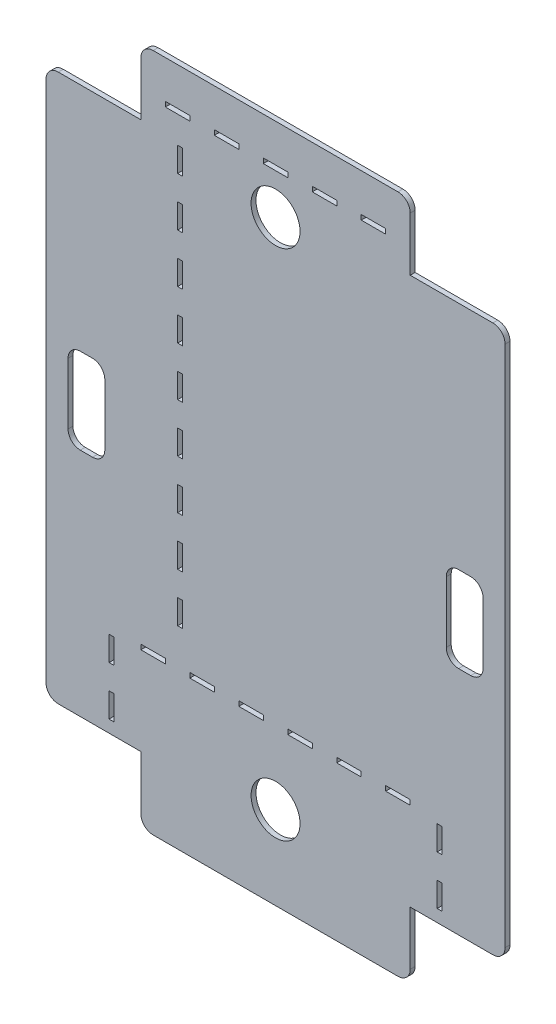
SolidWorks part; units mm, degrees
material "Verre"
ref_plane "Plan de face" through (0, 0, 0) normal (0, 0, 1) x (1, 0, 0)
ref_plane "Plan de dessus" through (0, 0, 0) normal (0, 1, 0) x (1, 0, 0)
ref_plane "Plan de droite" through (0, 0, 0) normal (1, 0, 0) x (0, 0, -1)
sketch "Esquisse1" plane through (0, 0, 0) normal (0, 0, 1) x (1, 0, 0)
  line L0 (-99.7487, 120) -> (-75, 144.7487)
  line L1 (-75, 144.7487) -> (75, 144.7487)
  line L2 (-99.7487, 120) -> (-99.7487, -120)
  line L3 (-75, -144.7487) -> (75, -144.7487)
  line L4 (99.7487, 120) -> (99.7487, -120)
  line L5 (75, 144.7487) -> (99.7487, 120)
  line L6 (99.7487, -120) -> (75, -144.7487)
  line L7 (-87.3744, 132.3744) -> (87.3744, -132.3744) construction
  line L8 (-99.7487, -120) -> (-75, -144.7487)
  line L9 (-87.3744, -132.3744) -> (87.3744, 132.3744) construction
  point P0 (0, 0)
  point P14 (0, 0)
  dimension "D1" = 240
  dimension "D2" = 150
  dimension "D3" = 35
  dimension "D4" = 135
  dimension "D5" = 135
extrude "Base" add sketch "Esquisse1" along normal blind 2
sketch "Esquisse2" plane through (0, 0, 2) normal (0, 0, 1) x (1, 0, 0)
  line L0 (-99.7487, 0) -> (99.7487, 0) construction
  line L1 (-99.7487, 120) -> (-99.7487, -120) construction
  line L2 (99.7487, -120) -> (99.7487, 120) construction
  line L3 (0, 144.7487) -> (0, -144.7487) construction
  line L4 (75, 144.7487) -> (-75, 144.7487) construction
  line L5 (-75, -144.7487) -> (75, -144.7487) construction
  line L6 (55, 131.7487) -> (55, 111.7487)
  line L7 (-75, 131.7487) -> (-55, 131.7487)
  line L8 (-75, 131.7487) -> (-75, 111.7487)
  line L9 (-75, 111.7487) -> (-55, 111.7487)
  line L10 (-55, 131.7487) -> (-55, 111.7487)
  line L11 (-75, 131.7487) -> (-55, 111.7487) construction
  line L12 (-75, 111.7487) -> (-55, 131.7487) construction
  line L13 (75, 111.7487) -> (55, 111.7487)
  line L14 (75, 131.7487) -> (75, 111.7487)
  line L15 (75, 131.7487) -> (55, 131.7487)
  line L16 (75, -111.7487) -> (55, -111.7487)
  line L17 (75, -131.7487) -> (75, -111.7487)
  line L18 (75, -131.7487) -> (55, -131.7487)
  line L19 (55, -131.7487) -> (55, -111.7487)
  line L20 (-55, -131.7487) -> (-55, -111.7487)
  line L21 (-75, -111.7487) -> (-55, -111.7487)
  line L22 (-75, -131.7487) -> (-75, -111.7487)
  line L23 (-75, -131.7487) -> (-55, -131.7487)
  point P12 (-65, 121.7487)
  dimension "D1" = 20
  dimension "D2" = 20
  dimension "D3" = 23
  dimension "D4" = 65
extrude "Perçage profilé" cut sketch "Esquisse2" against normal blind 5
sketch "Esquisse3" plane through (0, 0, 2) normal (0, 0, 1) x (1, 0, 0)
  line L0 (0, 144.7487) -> (0, -144.7487) construction
  line L1 (75, 144.7487) -> (-75, 144.7487) construction
  line L2 (-75, -144.7487) -> (75, -144.7487) construction
  line L3 (-99.7487, 0) -> (99.7487, 0) construction
  line L4 (-99.7487, 120) -> (-99.7487, -120) construction
  line L5 (99.7487, -120) -> (99.7487, 120) construction
  line L6 (79.7487, -17.5) -> (74.7487, -17.5)
  line L11 (-79.7487, 17.5) -> (-74.7487, 17.5)
  line L12 (-84.7487, 12.5) -> (-84.7487, -12.5)
  line L13 (-79.7487, -17.5) -> (-74.7487, -17.5)
  line L14 (-69.7487, 12.5) -> (-69.7487, -12.5)
  line L15 (-84.7487, 17.5) -> (-69.7487, -17.5) construction
  line L16 (-84.7487, -17.5) -> (-69.7487, 17.5) construction
  line L17 (84.7487, 12.5) -> (84.7487, -12.5)
  line L18 (79.7487, 17.5) -> (74.7487, 17.5)
  line L19 (69.7487, 12.5) -> (69.7487, -12.5)
  circle A0 centre (0, -104.7487) radius 10
  circle A1 centre (0, 104.7487) radius 10
  arc A2 (74.7487, -17.5) -> (69.7487, -12.5) centre (74.7487, -12.5) cw
  arc A3 (79.7487, -17.5) -> (84.7487, -12.5) centre (79.7487, -12.5) ccw
  arc A4 (84.7487, 12.5) -> (79.7487, 17.5) centre (79.7487, 12.5) ccw
  arc A5 (74.7487, 17.5) -> (69.7487, 12.5) centre (74.7487, 12.5) ccw
  arc A6 (-84.7487, -12.5) -> (-79.7487, -17.5) centre (-79.7487, -12.5) ccw
  arc A7 (-74.7487, -17.5) -> (-69.7487, -12.5) centre (-74.7487, -12.5) ccw
  arc A8 (-74.7487, 17.5) -> (-69.7487, 12.5) centre (-74.7487, 12.5) cw
  arc A9 (-79.7487, 17.5) -> (-84.7487, 12.5) centre (-79.7487, 12.5) ccw
  point P16 (-77.2487, 0)
  point P27 (69.7487, -17.5)
  point P30 (84.7487, -17.5)
  point P33 (84.7487, 17.5)
  point P36 (69.7487, 17.5)
  dimension "D1" = 20
  dimension "D6" = 5
  dimension "D2" = 15
  dimension "D3" = 35
  dimension "D4" = 40
  dimension "D5" = 15
extrude "Trous câble breadboard" cut sketch "Esquisse3" against normal blind 5
sketch "Sketch2" plane through (0, 0, 2) normal (0, 0, 1) x (1, 0, 0)
  line L0 (-55, 111.7487) -> (-55, 131.7487) construction
  line L1 (-45, 123.2487) -> (-35, 123.2487)
  line L2 (-45, 123.2487) -> (-45, 120.2487)
  line L3 (-45, 120.2487) -> (-35, 120.2487)
  line L4 (-35, 123.2487) -> (-35, 120.2487)
  line L5 (-75, 121.7487) -> (-55, 121.7487) construction
  line L6 (-75, 131.7487) -> (-75, 111.7487) construction
  line L7 (-45, 121.7487) -> (-35, 121.7487) construction
  line L8 (-25, 123.2487) -> (-25, 120.2487)
  line L9 (-25, 123.2487) -> (-15, 123.2487)
  line L10 (-15, 123.2487) -> (-15, 120.2487)
  line L11 (-25, 120.2487) -> (-15, 120.2487)
  line L12 (-5, 123.2487) -> (-5, 120.2487)
  line L13 (-5, 123.2487) -> (5, 123.2487)
  line L14 (5, 123.2487) -> (5, 120.2487)
  line L15 (-5, 120.2487) -> (5, 120.2487)
  line L16 (15, 123.2487) -> (15, 120.2487)
  line L17 (15, 123.2487) -> (25, 123.2487)
  line L18 (25, 123.2487) -> (25, 120.2487)
  line L19 (15, 120.2487) -> (25, 120.2487)
  line L20 (35, 123.2487) -> (35, 120.2487)
  line L21 (35, 123.2487) -> (45, 123.2487)
  line L22 (45, 123.2487) -> (45, 120.2487)
  line L23 (35, 120.2487) -> (45, 120.2487)
  line L24 (0, 0) -> (0, -37.251) construction
  line L25 (-68, -106.7487) -> (-65, -106.7487)
  line L26 (-68, -106.7487) -> (-68, -96.7487)
  line L27 (-68, -96.7487) -> (-65, -96.7487)
  line L28 (-65, -106.7487) -> (-65, -96.7487)
  line L29 (-55, -111.7487) -> (-75, -111.7487) construction
  line L30 (-66.5, -106.7487) -> (-66.5, -96.7487) construction
  line L31 (-40, 90.2487) -> (-40, 80.2487)
  line L32 (-40, 110.2487) -> (-37, 110.2487)
  line L33 (-68, -86.7487) -> (-68, -76.7487)
  line L34 (-68, -86.7487) -> (-65, -86.7487)
  line L35 (-65, -86.7487) -> (-65, -76.7487)
  line L36 (-68, -76.7487) -> (-65, -76.7487)
  line L37 (68, -86.7487) -> (65, -86.7487)
  line L38 (65, -86.7487) -> (65, -76.7487)
  line L39 (68, -76.7487) -> (65, -76.7487)
  line L40 (68, -86.7487) -> (68, -76.7487)
  line L41 (68, -96.7487) -> (65, -96.7487)
  line L42 (65, -106.7487) -> (65, -96.7487)
  line L43 (68, -106.7487) -> (65, -106.7487)
  line L44 (68, -106.7487) -> (68, -96.7487)
  line L45 (-35, -76.7487) -> (-35, -73.7487)
  line L46 (-55, -76.7487) -> (-45, -76.7487)
  line L47 (-55, -76.7487) -> (-55, -73.7487)
  line L48 (-55, -73.7487) -> (-45, -73.7487)
  line L49 (-45, -76.7487) -> (-45, -73.7487)
  line L50 (-35, -76.7487) -> (-25, -76.7487)
  line L51 (-25, -76.7487) -> (-25, -73.7487)
  line L52 (-35, -73.7487) -> (-25, -73.7487)
  line L53 (-15, -76.7487) -> (-15, -73.7487)
  line L54 (-15, -76.7487) -> (-5, -76.7487)
  line L55 (-5, -76.7487) -> (-5, -73.7487)
  line L56 (-15, -73.7487) -> (-5, -73.7487)
  line L57 (5, -76.7487) -> (5, -73.7487)
  line L58 (5, -76.7487) -> (15, -76.7487)
  line L59 (15, -76.7487) -> (15, -73.7487)
  line L60 (5, -73.7487) -> (15, -73.7487)
  line L61 (25, -76.7487) -> (25, -73.7487)
  line L62 (25, -76.7487) -> (35, -76.7487)
  line L63 (35, -76.7487) -> (35, -73.7487)
  line L64 (25, -73.7487) -> (35, -73.7487)
  line L65 (45, -76.7487) -> (45, -73.7487)
  line L66 (45, -76.7487) -> (55, -76.7487)
  line L67 (55, -76.7487) -> (55, -73.7487)
  line L68 (45, -73.7487) -> (55, -73.7487)
  line L69 (-40, 110.2487) -> (-40, 100.2487)
  line L70 (-40, 100.2487) -> (-37, 100.2487)
  line L71 (-37, 110.2487) -> (-37, 100.2487)
  line L72 (-40, 90.2487) -> (-37, 90.2487)
  line L73 (-37, 90.2487) -> (-37, 80.2487)
  line L74 (-40, 80.2487) -> (-37, 80.2487)
  line L75 (-40, 70.2487) -> (-40, 60.2487)
  line L76 (-40, 70.2487) -> (-37, 70.2487)
  line L77 (-37, 70.2487) -> (-37, 60.2487)
  line L78 (-40, 60.2487) -> (-37, 60.2487)
  line L79 (-40, 50.2487) -> (-40, 40.2487)
  line L80 (-40, 50.2487) -> (-37, 50.2487)
  line L81 (-37, 50.2487) -> (-37, 40.2487)
  line L82 (-40, 40.2487) -> (-37, 40.2487)
  line L83 (-40, 30.2487) -> (-40, 20.2487)
  line L84 (-40, 30.2487) -> (-37, 30.2487)
  line L85 (-37, 30.2487) -> (-37, 20.2487)
  line L86 (-40, 20.2487) -> (-37, 20.2487)
  line L87 (-40, 10.2487) -> (-40, 0.2487)
  line L88 (-40, 10.2487) -> (-37, 10.2487)
  line L89 (-37, 10.2487) -> (-37, 0.2487)
  line L90 (-40, 0.2487) -> (-37, 0.2487)
  line L91 (-40, -9.7513) -> (-40, -19.7513)
  line L92 (-40, -9.7513) -> (-37, -9.7513)
  line L93 (-37, -9.7513) -> (-37, -19.7513)
  line L94 (-40, -19.7513) -> (-37, -19.7513)
  line L95 (-40, -29.7513) -> (-40, -39.7513)
  line L96 (-40, -29.7513) -> (-37, -29.7513)
  line L97 (-37, -29.7513) -> (-37, -39.7513)
  line L98 (-40, -39.7513) -> (-37, -39.7513)
  line L99 (-40, -49.7513) -> (-40, -59.7513)
  line L100 (-40, -49.7513) -> (-37, -49.7513)
  line L101 (-37, -49.7513) -> (-37, -59.7513)
  line L102 (-40, -59.7513) -> (-37, -59.7513)
  dimension "D1" = 10
  dimension "D2" = 3
  dimension "D3" = 10
  dimension "D4" = 10
  dimension "D5" = 3
  dimension "D6" = 5
  dimension "D8" = 10
  dimension "D9" = 3
  dimension "D10" = 10
  dimension "D11" = 65
  dimension "D12" = 10
  dimension "D13" = 5
  dimension "D14" = 10
  dimension "D15" = 3
  dimension "D16" = 15
  dimension "D7" = 2
  dimension "D17" = 9
extrude "Cut-Extrude1" cut sketch "Sketch2" against normal through all
sketch "Esquisse5" plane through (0, 0, 2) normal (0, 0, 1) x (1, 0, 0)
  line L0 (-72.5147, 138.7487) -> (72.5147, 138.7487)
  line L1 (72.5147, 138.7487) -> (93.7487, 117.5147)
  line L2 (93.7487, 117.5147) -> (93.7487, -117.5147)
  line L3 (93.7487, -117.5147) -> (72.5147, -138.7487)
  line L4 (72.5147, -138.7487) -> (-72.5147, -138.7487)
  line L5 (-72.5147, -138.7487) -> (-93.7487, -117.5147)
  line L6 (-93.7487, -117.5147) -> (-93.7487, 117.5147)
  line L7 (-93.7487, 117.5147) -> (-72.5147, 138.7487)
  line L8 (75, 144.7487) -> (-75, 144.7487) construction
  line L9 (99.7487, 120) -> (75, 144.7487) construction
  line L10 (99.7487, -120) -> (99.7487, 120) construction
  line L11 (75, -144.7487) -> (99.7487, -120) construction
  line L12 (-75, -144.7487) -> (75, -144.7487) construction
  line L13 (-99.7487, -120) -> (-75, -144.7487) construction
  line L14 (-99.7487, 120) -> (-99.7487, -120) construction
  line L15 (-75, 144.7487) -> (-99.7487, 120) construction
  line L16 (-16.6743, 205.0451) -> (192.8195, 199.3251)
  line L17 (192.8195, 199.3251) -> (168.5096, -212.5125)
  line L18 (168.5096, -212.5125) -> (-168.9684, -176.7627)
  line L19 (-168.9684, -176.7627) -> (-185.4133, 175.0153)
  line L20 (-185.4133, 175.0153) -> (-16.6743, 205.0451)
  point P25 (-87.3744, 132.3744)
  dimension "D1" = 6
  dimension "D2" = 6
  dimension "D3" = 6
  dimension "D4" = 6
  dimension "D5" = 6
  dimension "D6" = 6
  dimension "D7" = 6
  dimension "D8" = 6
extrude "Enlèv. mat.-Extru.1" cut sketch "Esquisse5" against normal through all
sketch "Esquisse6" plane through (0, 0, 2) normal (0, 0, 1) x (1, 0, 0)
  line L0 (-55, 111.7487) -> (-55, 131.7487) construction
  line L1 (-55, 152.8346) -> (-122.6187, 152.8346)
  line L2 (-55, 152.8346) -> (-55, 111.7487)
  line L3 (-55, 111.7487) -> (-122.6187, 111.7487)
  line L4 (-122.6187, 152.8346) -> (-122.6187, 111.7487)
  line L6 (55, 131.7487) -> (55, 111.7487) construction
  line L7 (55, 111.7487) -> (108.2306, 111.7487)
  line L8 (55, 111.7487) -> (55, 146.7402)
  line L9 (55, 146.7402) -> (108.2306, 146.7402)
  line L10 (108.2306, 111.7487) -> (108.2306, 146.7402)
  line L13 (128.1315, -111.7487) -> (55, -111.7487)
  line L14 (128.1315, -111.7487) -> (128.1315, -148.2847)
  line L15 (128.1315, -148.2847) -> (55, -148.2847)
  line L16 (55, -111.7487) -> (55, -148.2847)
  line L17 (55, -111.7487) -> (55, -131.7487) construction
  line L19 (-104.2886, -111.7487) -> (-55, -111.7487)
  line L20 (-104.2886, -111.7487) -> (-104.2886, -146.9826)
  line L21 (-104.2886, -146.9826) -> (-55, -146.9826)
  line L22 (-55, -111.7487) -> (-55, -146.9826)
  line L23 (-55, -131.7487) -> (-55, -111.7487) construction
  line L24 (-55, -111.7487) -> (-75, -111.7487) construction
  line L25 (-75, 111.7487) -> (-55, 111.7487) construction
  line L26 (55, 111.7487) -> (75, 111.7487) construction
  line L27 (75, -111.7487) -> (55, -111.7487) construction
extrude "Enlèv. mat.-Extru.2" cut sketch "Esquisse6" against normal through all
fillet "Congé2" radius 5 4 edges at (55, -138.7487, 1) (-55, -138.7487, 1) (-55, 138.7487, 1) (55, 138.7487, 1)
sketch "Esquisse4" plane through (0, 0, 2) normal (0, 0, 1) x (1, 0, 0)
  line L1 (99.7487, 62.0019) -> (62.7487, 62.0019)
  line L2 (99.7487, 62.0019) -> (99.7487, -32.9981)
  line L3 (99.7487, -32.9981) -> (62.7487, -32.9981)
  line L4 (62.7487, 62.0019) -> (62.7487, -32.9981)
  line L5 (41.9383, 53.5019) -> (39.3294, 53.5019) construction
  line L6 (38.7442, 53.5019) -> (38.7442, 62.0019) construction
  line L7 (84.0538, -24.4981) -> (84.0538, -32.9981) construction
  line L8 (49.6874, -24.4981) -> (43.4757, -24.4981) construction
  line L10 (62.7487, 62.0019) -> (29.7487, 62.0019)
  line L11 (62.7487, 62.0019) -> (62.7487, 29.0019)
  line L12 (62.7487, 29.0019) -> (29.7487, 29.0019)
  line L13 (29.7487, 62.0019) -> (29.7487, 29.0019)
  line L14 (93.7487, -111.7487) -> (93.7487, 111.7487) construction
  dimension "D1" = 95
  dimension "D2" = 37
  dimension "D3" = 33
  dimension "D4" = 33
  dimension "D5" = 6
sketch "Esquisse7" plane through (0, 0, 2) normal (0, 0, 1) x (1, 0, 0)
  line L0 (-40, -59.7513) -> (-37, -59.7513) construction
  line L1 (-37, 110.2487) -> (-38, 110.2487)
  line L2 (-37, 110.2487) -> (-37, -59.7513)
  line L3 (-37, -59.7513) -> (-38, -59.7513)
  line L4 (-38, 110.2487) -> (-38, -59.7513)
  line L5 (-68, -106.7487) -> (-65, -106.7487) construction
  line L6 (-65, -76.7487) -> (-66, -76.7487)
  line L7 (-65, -76.7487) -> (-65, -106.7487)
  line L8 (-65, -106.7487) -> (-66, -106.7487)
  line L9 (-66, -76.7487) -> (-66, -106.7487)
  line L10 (65, -106.7487) -> (68, -106.7487) construction
  line L11 (65, -76.7487) -> (66, -76.7487)
  line L12 (65, -76.7487) -> (65, -106.7487)
  line L13 (65, -106.7487) -> (66, -106.7487)
  line L14 (66, -76.7487) -> (66, -106.7487)
  line L20 (45, 120.2487) -> (45, 123.2487) construction
  line L21 (-45, 120.2487) -> (45, 120.2487)
  line L22 (-45, 120.2487) -> (-45, 121.2487)
  line L23 (-45, 121.2487) -> (45, 121.2487)
  line L24 (45, 120.2487) -> (45, 121.2487)
  line L30 (55, -76.7487) -> (55, -73.7487) construction
  line L31 (-55, -76.7487) -> (55, -76.7487)
  line L32 (-55, -76.7487) -> (-55, -75.7487)
  line L33 (-55, -75.7487) -> (55, -75.7487)
  line L34 (55, -76.7487) -> (55, -75.7487)
  dimension "D1" = 1
extrude "Boss.-Extru.1" add sketch "Esquisse7" against normal blind 2
fillet "Congé3" radius 5 4 edges at (-93.7487, -111.7487, 1) (93.7487, -111.7487, 1) (93.7487, 111.7487, 1) (-93.7487, 111.7487, 1)
